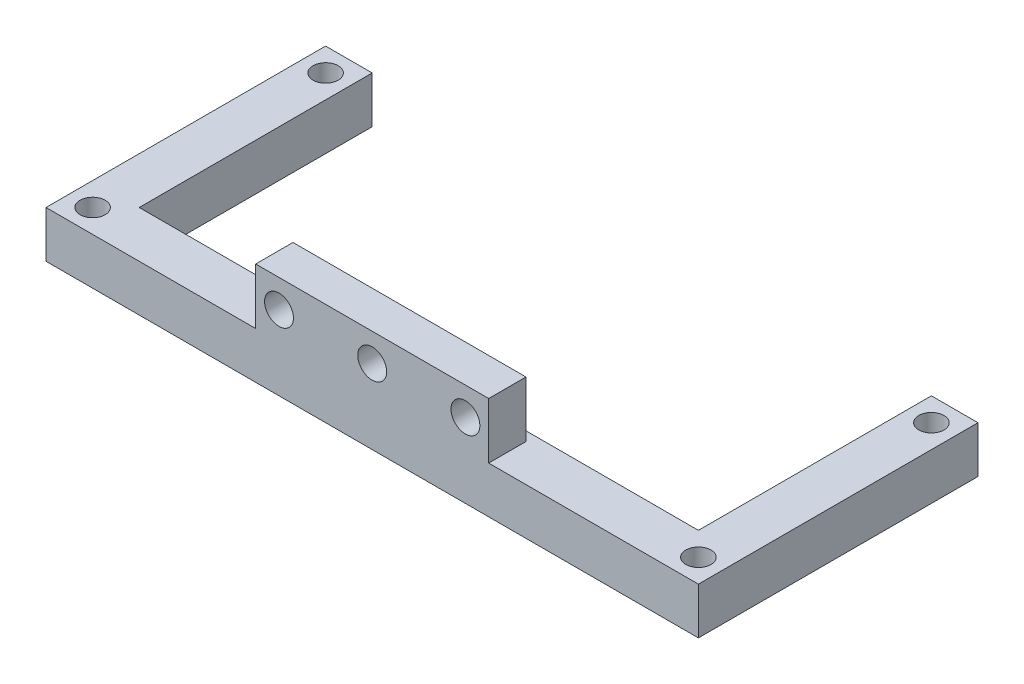
SolidWorks part; units mm, degrees
ref_plane "Front Plane" through (0, 0, 0) normal (0, 0, 1) x (1, 0, 0)
ref_plane "Top Plane" through (0, 0, 0) normal (0, 1, 0) x (1, 0, 0)
ref_plane "Right Plane" through (0, 0, 0) normal (1, 0, 0) x (0, 0, -1)
sketch "Sketch1" plane through (0, 0, 0) normal (0, 1, 0) x (1, 0, 0)
  line L1 (35, -15) -> (-35, -15)
  line L2 (35, -15) -> (35, 15)
  line L3 (35, 15) -> (-35, 15)
  line L4 (-35, -15) -> (-35, 15)
  line L5 (35, -15) -> (-35, 15) construction
  line L6 (35, 15) -> (-35, -15) construction
  point P0 (0, 0)
  dimension "D1" = 30
  dimension "D2" = 70
extrude "Boss-Extrude1" add sketch "Sketch1" along normal blind 5
sketch "Sketch2" plane through (0, 5, 0) normal (0, 1, 0) x (1, 0, 0)
  line L8 (-32.5, 12.5) -> (32.5, 12.5)
  line L9 (-32.5, 12.5) -> (-32.5, -12.5)
  line L10 (-32.5, -12.5) -> (32.5, -12.5)
  line L11 (32.5, 12.5) -> (32.5, -12.5)
  line L12 (-32.5, 12.5) -> (32.5, -12.5) construction
  line L13 (-32.5, -12.5) -> (32.5, 12.5) construction
  circle A3 centre (-32.5, 12.5) radius 1.35
  circle A4 centre (32.5, 12.5) radius 1.35
  circle A5 centre (-32.5, -12.5) radius 1.35
  circle A6 centre (32.5, -12.5) radius 1.35
  point P0 (0, 0)
  dimension "D1" = 25
  dimension "D3" = 2.7
  dimension "D4" = 2.7
  dimension "D5" = 2.7
  dimension "D6" = 2.7
  dimension "D2" = 65
extrude "Cut-Extrude1" cut sketch "Sketch2" against normal through all contours A3 | A5 | A6 | A4
sketch "Sketch3" plane through (0, 5, 0) normal (0, 1, 0) x (1, 0, 0)
  line L0 (12.5, -15) -> (12.5, -11)
  line L1 (-35, -15) -> (35, -15) construction
  line L2 (12.5, -11) -> (-12.5, -11)
  line L3 (-12.5, -11) -> (-12.5, -15)
  line L4 (-12.5, -15) -> (12.5, -15)
  line L5 (-35, 15) -> (-35, -15) construction
  point P5 (0, -11)
  dimension "D1" = 35
  dimension "D2" = 25
  dimension "D3" = 4
extrude "Boss-Extrude2" add sketch "Sketch3" along normal blind 6
sketch "Sketch4" plane through (0, 0, 11) normal (0, 0, -1) x (-1, 0, 0)
  line L0 (-12.5, 11) -> (-12.5, 5) construction
  line L1 (-12.5, 11) -> (12.5, 11) construction
  circle A0 centre (-10, 8) radius 1.55
  circle A1 centre (0, 8) radius 1.55
  circle A2 centre (10, 8) radius 1.55
  dimension "D1" = 3
  dimension "D2" = 2.5
  dimension "D3" = 3
extrude "Cut-Extrude2" cut sketch "Sketch4" against normal through all
sketch "Sketch5" plane through (0, 5, 0) normal (0, 1, 0) x (1, 0, 0)
  line L0 (-30, 15) -> (-30, -10)
  line L1 (35, 15) -> (-35, 15) construction
  line L2 (-30, -10) -> (30, -10)
  line L3 (30, -10) -> (30, 15)
  line L4 (30, 15) -> (-30, 15)
  line L5 (-35, 15) -> (-35, -15) construction
  point P6 (0, 15)
  dimension "D1" = 60
  dimension "D2" = 25
  dimension "D3" = 35
extrude "Cut-Extrude3" cut sketch "Sketch5" against normal through all
